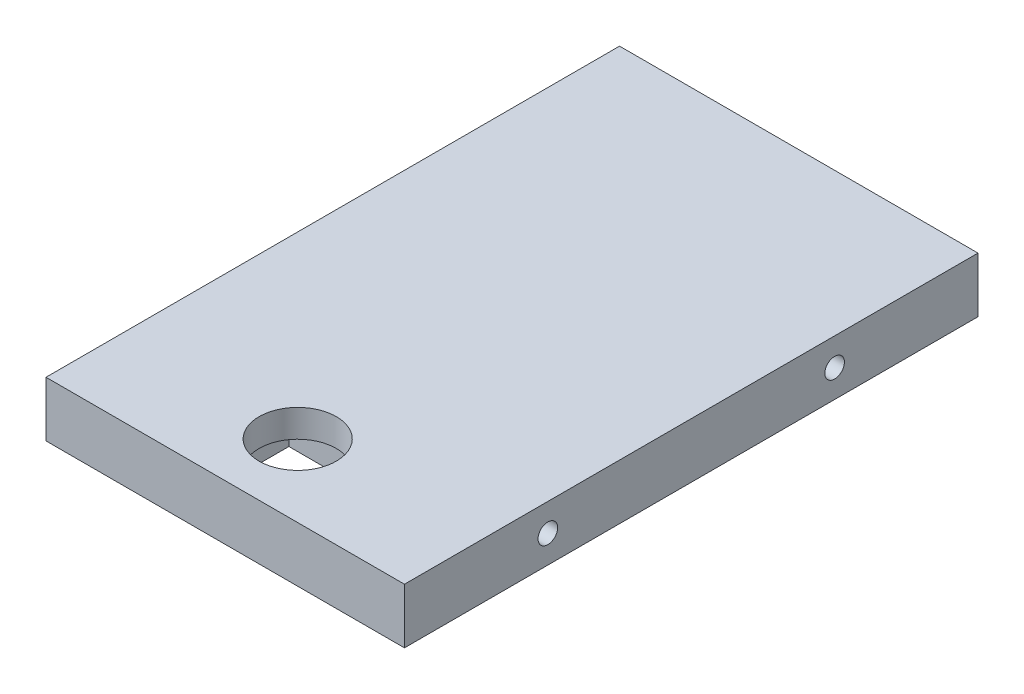
SolidWorks part; units mm, degrees
ref_plane "Front Plane" through (0, 0, 0) normal (0, 0, 1) x (1, 0, 0)
ref_plane "Top Plane" through (0, 0, 0) normal (0, 1, 0) x (1, 0, 0)
ref_plane "Right Plane" through (0, 0, 0) normal (1, 0, 0) x (0, 0, -1)
sketch "Sketch1" plane through (0, 0, 0) normal (0, 1, 0) x (1, 0, 0)
  line L1 (0, 0) -> (32.5, 0)
  line L2 (0, 0) -> (0, 52)
  line L3 (0, 52) -> (32.5, 52)
  line L4 (32.5, 0) -> (32.5, 52)
extrude "Boss-Extrude1" add sketch "Sketch1" along normal blind 5
sketch "Sketch2" plane through (0, 5, 0) normal (0, 1, 0) x (1, 0, 0)
  line L0 (0, 0) -> (0, 3)
  line L1 (0, 52) -> (0, 0) construction
  line L2 (0, 3) -> (32.5, 3)
  line L3 (32.5, 0) -> (32.5, 52) construction
  line L4 (0, 1.5) -> (32.5, 1.5)
  line L5 (16.25, 3) -> (0, 0)
  line L6 (16.25, 3) -> (32.5, 0)
  line L7 (0, 52) -> (0, 45)
  line L8 (0, 45) -> (32.5, 45)
  line L9 (0, 48.5) -> (32.5, 48.5)
  line L10 (0, 52) -> (16.25, 45)
  line L11 (16.25, 45) -> (32.5, 52)
sketch "Sketch3" plane through (0, 5, 0) normal (0, 1, 0) x (1, 0, 0)
  line L0 (0, 52) -> (16.25, 45) construction
  line L1 (16.25, 45) -> (32.5, 52) construction
  line L2 (16.25, 3) -> (0, 0) construction
  line L3 (16.25, 3) -> (32.5, 0) construction
  circle A0 centre (8.125, 48.5) radius 1.22
  circle A1 centre (24.375, 48.5) radius 1.22
  circle A2 centre (8.125, 1.5) radius 1.22
  circle A3 centre (24.375, 1.5) radius 1.22
sketch "Sketch4" plane through (0, 0, 0) normal (-1, 0, 0) x (0, 0, 1)
  line L0 (-52, 5) -> (-26, 0)
  line L1 (-52, 0) -> (0, 0) construction
  line L2 (-26, 0) -> (0, 5)
  line L3 (0, 5) -> (0, 0)
  line L4 (0, 0) -> (-26, 5)
  line L5 (-52, 5) -> (0, 5) construction
  line L6 (-26, 5) -> (-52, 0)
hole_wizard "#2-56 Tapped Hole1" positions "Sketch5" profile "Sketch6" tap size "#2-56" standard "ANSI Inch"
sketch "Sketch5" plane through (0, 0, 0) normal (-1, 0, 0) x (0, 0, 1)
  line L0 (-52, 5) -> (-26, 0) construction
  line L1 (-26, 0) -> (0, 5) construction
  point P0 (-39, 2.5)
  point P4 (-13, 2.5)
sketch "Sketch6" plane through (0, 2.5, -39) normal (0, 1, 0) x (0, 0, 1)
  line L0 (0, 0) -> (0, 8)
  line L1 (0, 8) -> (0.889, 7.4658)
  line L2 (0.889, 7.4658) -> (0.889, 0)
  line L5 (0.889, 0) -> (0, 0)
  line L10 (0, 8) -> (-0.889, 7.4658) construction
  line L11 (0, -6.35) -> (0, 107.95) construction
  dimension "Tap Drill Dia." = 1.778
  dimension "Tap Drill Depth" = 8
  dimension "Drill Angle" = 118
cosmetic thread "Hole Thread1" parameters "D1"=4.37, "D2"=2.1844
cosmetic thread "Hole Thread2" parameters "D1"=4.37, "D2"=2.1844
sketch "Sketch7" plane through (32.5, 0, 0) normal (1, 0, 0) x (0, 0, -1)
  line L0 (0, 5) -> (26, 0)
  line L1 (0, 0) -> (52, 0) construction
  line L2 (26, 0) -> (52, 5)
  line L3 (52, 5) -> (52, 0)
  line L4 (52, 0) -> (26, 5)
  line L5 (0, 5) -> (52, 5) construction
  line L6 (26, 5) -> (0, 0)
hole_wizard "#2-56 Tapped Hole2" positions "Sketch8" profile "Sketch9" tap size "#2-56" standard "ANSI Inch"
sketch "Sketch8" plane through (32.5, 0, 0) normal (1, 0, 0) x (0, 0, -1)
  line L0 (0, 5) -> (26, 0) construction
  line L1 (26, 0) -> (52, 5) construction
  point P0 (13, 2.5)
  point P4 (39, 2.5)
sketch "Sketch9" plane through (32.5, 2.5, -13) normal (0, 1, 0) x (0, 0, -1)
  line L0 (0, 0) -> (0, 8)
  line L1 (0, 8) -> (0.889, 7.4658)
  line L2 (0.889, 7.4658) -> (0.889, 0)
  line L5 (0.889, 0) -> (0, 0)
  line L10 (0, 8) -> (-0.889, 7.4658) construction
  line L11 (0, -6.35) -> (0, 107.95) construction
  dimension "Tap Drill Dia." = 1.778
  dimension "Tap Drill Depth" = 8
  dimension "Drill Angle" = 118
cosmetic thread "Hole Thread3" parameters "D1"=4.37, "D2"=2.1844
cosmetic thread "Hole Thread4" parameters "D1"=4.37, "D2"=2.1844
sketch "Sketch10" plane through (0, 5, 0) normal (0, 1, 0) x (1, 0, 0)
  line L0 (0, 0) -> (0, 6.57)
  line L1 (0, 52) -> (0, 0) construction
  line L2 (0, 6.57) -> (32.5, 6.57)
  line L3 (32.5, 0) -> (32.5, 52) construction
  circle A0 centre (16.25, 6.57) radius 3.5
sketch "Sketch11" plane through (0, 0, 0) normal (0, -1, 0) x (-1, 0, 0)
  line L1 (0, 6.57) -> (-32.5, 6.57) construction
  line L2 (-21.05, 6.57) -> (-21.05, 10.57)
  line L3 (-21.05, 10.57) -> (-11.45, 10.57)
  line L4 (-11.45, 10.57) -> (-11.45, 2.57)
  line L5 (-11.45, 2.57) -> (-21.05, 2.57)
  line L6 (-21.05, 2.57) -> (-21.05, 6.57)
  point P0 (0, 0)
extrude "Cut-Extrude2" cut sketch "Sketch11" against normal blind 2.5
extrude "Cut-Extrude3" cut sketch "Sketch10" against normal blind 2.5 contours A0
